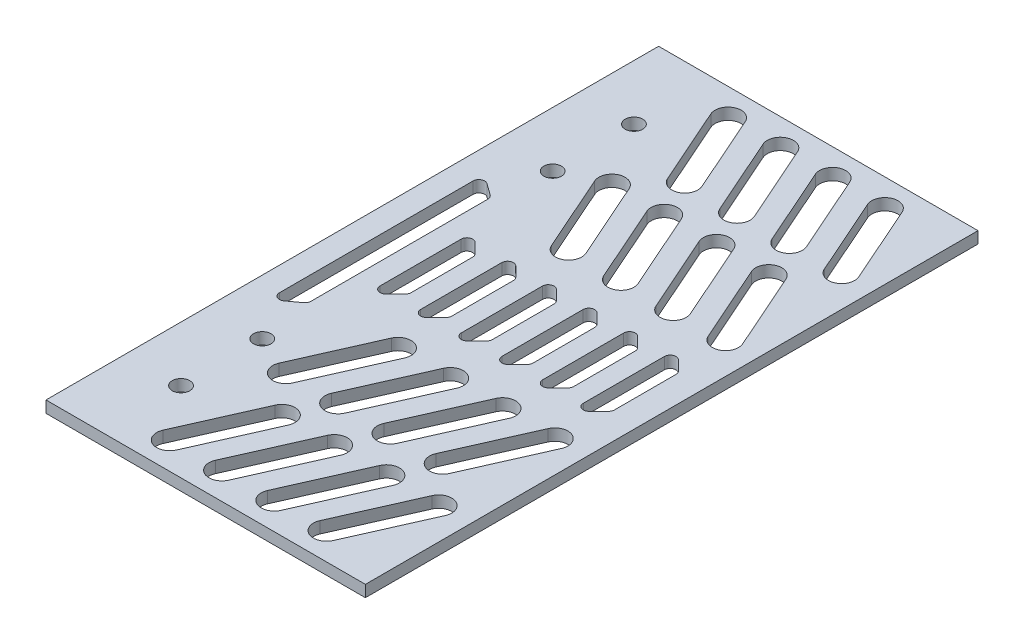
SolidWorks part; units mm, degrees
material "Thornel Mat VMA"
ref_plane "前视基准面" through (0, 0, 0) normal (0, 0, 1) x (1, 0, 0)
ref_plane "上视基准面" through (0, 0, 0) normal (0, 1, 0) x (1, 0, 0)
ref_plane "右视基准面" through (0, 0, 0) normal (1, 0, 0) x (0, 0, -1)
sketch "草图1" plane through (0, 0, 0) normal (0, 0, 1) x (1, 0, 0)
  line L2 (0, 30) -> (-55, 30)
  line L3 (0, 28) -> (-55, 28)
  line L4 (-55, 28) -> (-55, 30)
  line L5 (0, 0) -> (0, 30) construction
  line L6 (0, 30) -> (0, 28)
  dimension "D1" = 55
  dimension "D2" = 2
extrude "凸台-拉伸1" add sketch "草图1" along normal blind 105.5
sketch "草图2" plane through (0, 30, 0) normal (0, 1, 0) x (1, 0, 0)
  line L0 (-55, -105.5) -> (-55, 0) construction
  line L1 (0, -105.5) -> (-55, -105.5) construction
  line L2 (0, 0) -> (-55, 0) construction
  line L3 (-115.243, -52.75) -> (60.545, -52.75) construction
  line L4 (0, -105.5) -> (-55, -105.5) construction
  line L5 (-11.361, -4.6755) -> (-5.4387, -18.0556) construction
  line L6 (-9.3031, -3.7646) -> (-3.3807, -17.1447)
  line L7 (-13.419, -5.5864) -> (-7.4967, -18.9665)
  line L8 (-20.361, -4.6755) -> (-14.4387, -18.0556) construction
  line L9 (-18.3031, -3.7646) -> (-12.3807, -17.1447)
  line L10 (-22.419, -5.5864) -> (-16.4967, -18.9665)
  line L11 (-29.361, -4.6755) -> (-23.4387, -18.0556) construction
  line L12 (-27.3031, -3.7646) -> (-21.3807, -17.1447)
  line L13 (-31.419, -5.5864) -> (-25.4967, -18.9665)
  line L14 (-38.361, -4.6755) -> (-32.4387, -18.0556) construction
  line L15 (-36.3031, -3.7646) -> (-30.3807, -17.1447)
  line L16 (-40.419, -5.5864) -> (-34.4967, -18.9665)
  line L17 (-11.361, -24.6755) -> (-5.4387, -38.0556) construction
  line L18 (-9.3031, -23.7646) -> (-3.3807, -37.1447)
  line L19 (-13.419, -25.5864) -> (-7.4967, -38.9665)
  line L20 (-20.361, -24.6755) -> (-14.4387, -38.0556) construction
  line L21 (-18.3031, -23.7646) -> (-12.3807, -37.1447)
  line L22 (-22.419, -25.5864) -> (-16.4967, -38.9665)
  line L23 (-29.361, -24.6755) -> (-23.4387, -38.0556) construction
  line L24 (-27.3031, -23.7646) -> (-21.3807, -37.1447)
  line L25 (-31.419, -25.5864) -> (-25.4967, -38.9665)
  line L26 (-38.361, -24.6755) -> (-32.4387, -38.0556) construction
  line L27 (-36.3031, -23.7646) -> (-30.3807, -37.1447)
  line L28 (-40.419, -25.5864) -> (-34.4967, -38.9665)
  line L29 (-11.361, -80.8245) -> (-5.4387, -67.4444) construction
  line L30 (-9.3031, -81.7354) -> (-3.3807, -68.3553)
  line L31 (-13.419, -79.9136) -> (-7.4967, -66.5335)
  line L32 (-20.361, -80.8245) -> (-14.4387, -67.4444) construction
  line L33 (-18.3031, -81.7354) -> (-12.3807, -68.3553)
  line L34 (-22.419, -79.9136) -> (-16.4967, -66.5335)
  line L35 (-29.361, -80.8245) -> (-23.4387, -67.4444) construction
  line L36 (-27.3031, -81.7354) -> (-21.3807, -68.3553)
  line L37 (-31.419, -79.9136) -> (-25.4967, -66.5335)
  line L38 (-38.361, -80.8245) -> (-32.4387, -67.4444) construction
  line L39 (-36.3031, -81.7354) -> (-30.3807, -68.3553)
  line L40 (-40.419, -79.9136) -> (-34.4967, -66.5335)
  line L41 (-38.361, -100.8245) -> (-32.4387, -87.4444) construction
  line L42 (-36.3031, -101.7354) -> (-30.3807, -88.3553)
  line L43 (-40.419, -99.9136) -> (-34.4967, -86.5335)
  line L44 (-29.361, -100.8245) -> (-23.4387, -87.4444) construction
  line L45 (-27.3031, -101.7354) -> (-21.3807, -88.3553)
  line L46 (-31.419, -99.9136) -> (-25.4967, -86.5335)
  line L47 (-20.361, -100.8245) -> (-14.4387, -87.4444) construction
  line L48 (-18.3031, -101.7354) -> (-12.3807, -88.3553)
  line L49 (-22.419, -99.9136) -> (-16.4967, -86.5335)
  line L50 (-11.361, -100.8245) -> (-5.4387, -87.4444) construction
  line L51 (-9.3031, -101.7354) -> (-3.3807, -88.3553)
  line L52 (-13.419, -99.9136) -> (-7.4967, -86.5335)
  line L53 (-50.8884, -69.4318) -> (-50.8884, -36.0682)
  line L54 (-49.3025, -35.2578) -> (-47.3142, -36.6955)
  line L55 (-46.9001, -37.5059) -> (-46.9001, -67.9941)
  line L56 (-43.2424, -59.7286) -> (-43.2424, -45.7714)
  line L57 (-41.5353, -45.0643) -> (-39.857, -46.7426)
  line L58 (-39.5641, -47.4497) -> (-39.5641, -58.0503)
  line L59 (-41.5353, -60.4357) -> (-39.857, -58.7574)
  line L60 (-49.3025, -70.2422) -> (-47.3142, -68.8045)
  line L61 (-34.5353, -60.4357) -> (-32.857, -58.7574)
  line L62 (-36.2424, -59.7286) -> (-36.2424, -45.7714)
  line L63 (-34.5353, -45.0643) -> (-32.857, -46.7426)
  line L64 (-32.5641, -47.4497) -> (-32.5641, -58.0503)
  line L65 (-27.5353, -60.4357) -> (-25.857, -58.7574)
  line L66 (-29.2424, -59.7286) -> (-29.2424, -45.7714)
  line L67 (-27.5353, -45.0643) -> (-25.857, -46.7426)
  line L68 (-25.5641, -47.4497) -> (-25.5641, -58.0503)
  line L69 (-20.5353, -60.4357) -> (-18.857, -58.7574)
  line L70 (-22.2424, -59.7286) -> (-22.2424, -45.7714)
  line L71 (-20.5353, -45.0643) -> (-18.857, -46.7426)
  line L72 (-18.5641, -47.4497) -> (-18.5641, -58.0503)
  line L73 (-13.5353, -60.4357) -> (-11.857, -58.7574)
  line L74 (-15.2424, -59.7286) -> (-15.2424, -45.7714)
  line L75 (-13.5353, -45.0643) -> (-11.857, -46.7426)
  line L76 (-11.5641, -47.4497) -> (-11.5641, -58.0503)
  line L77 (-6.5353, -60.4357) -> (-4.857, -58.7574)
  line L78 (-8.2424, -59.7286) -> (-8.2424, -45.7714)
  line L79 (-6.5353, -45.0643) -> (-4.857, -46.7426)
  line L80 (-4.5641, -47.4497) -> (-4.5641, -58.0503)
  circle A0 centre (-45.5, -13.75) radius 1.51
  circle A1 centre (-45.5, -27.75) radius 1.51
  circle A2 centre (-45.5, -77.75) radius 1.51
  circle A3 centre (-45.5, -91.75) radius 1.51
  arc A4 (-9.3031, -3.7646) -> (-13.419, -5.5864) centre (-11.361, -4.6755) ccw
  arc A5 (-7.4967, -18.9665) -> (-3.3807, -17.1447) centre (-5.4387, -18.0556) ccw
  arc A6 (-18.3031, -3.7646) -> (-22.419, -5.5864) centre (-20.361, -4.6755) ccw
  arc A7 (-16.4967, -18.9665) -> (-12.3807, -17.1447) centre (-14.4387, -18.0556) ccw
  arc A8 (-27.3031, -3.7646) -> (-31.419, -5.5864) centre (-29.361, -4.6755) ccw
  arc A9 (-25.4967, -18.9665) -> (-21.3807, -17.1447) centre (-23.4387, -18.0556) ccw
  arc A10 (-36.3031, -3.7646) -> (-40.419, -5.5864) centre (-38.361, -4.6755) ccw
  arc A11 (-34.4967, -18.9665) -> (-30.3807, -17.1447) centre (-32.4387, -18.0556) ccw
  arc A12 (-9.3031, -23.7646) -> (-13.419, -25.5864) centre (-11.361, -24.6755) ccw
  arc A13 (-7.4967, -38.9665) -> (-3.3807, -37.1447) centre (-5.4387, -38.0556) ccw
  arc A14 (-18.3031, -23.7646) -> (-22.419, -25.5864) centre (-20.361, -24.6755) ccw
  arc A15 (-16.4967, -38.9665) -> (-12.3807, -37.1447) centre (-14.4387, -38.0556) ccw
  arc A16 (-27.3031, -23.7646) -> (-31.419, -25.5864) centre (-29.361, -24.6755) ccw
  arc A17 (-25.4967, -38.9665) -> (-21.3807, -37.1447) centre (-23.4387, -38.0556) ccw
  arc A18 (-36.3031, -23.7646) -> (-40.419, -25.5864) centre (-38.361, -24.6755) ccw
  arc A19 (-34.4967, -38.9665) -> (-30.3807, -37.1447) centre (-32.4387, -38.0556) ccw
  arc A20 (-9.3031, -81.7354) -> (-13.419, -79.9136) centre (-11.361, -80.8245) cw
  arc A21 (-7.4967, -66.5335) -> (-3.3807, -68.3553) centre (-5.4387, -67.4444) cw
  arc A22 (-18.3031, -81.7354) -> (-22.419, -79.9136) centre (-20.361, -80.8245) cw
  arc A23 (-16.4967, -66.5335) -> (-12.3807, -68.3553) centre (-14.4387, -67.4444) cw
  arc A24 (-27.3031, -81.7354) -> (-31.419, -79.9136) centre (-29.361, -80.8245) cw
  arc A25 (-25.4967, -66.5335) -> (-21.3807, -68.3553) centre (-23.4387, -67.4444) cw
  arc A26 (-36.3031, -81.7354) -> (-40.419, -79.9136) centre (-38.361, -80.8245) cw
  arc A27 (-34.4967, -66.5335) -> (-30.3807, -68.3553) centre (-32.4387, -67.4444) cw
  arc A28 (-36.3031, -101.7354) -> (-40.419, -99.9136) centre (-38.361, -100.8245) cw
  arc A29 (-34.4967, -86.5335) -> (-30.3807, -88.3553) centre (-32.4387, -87.4444) cw
  arc A30 (-27.3031, -101.7354) -> (-31.419, -99.9136) centre (-29.361, -100.8245) cw
  arc A31 (-25.4967, -86.5335) -> (-21.3807, -88.3553) centre (-23.4387, -87.4444) cw
  arc A32 (-18.3031, -101.7354) -> (-22.419, -99.9136) centre (-20.361, -100.8245) cw
  arc A33 (-16.4967, -86.5335) -> (-12.3807, -88.3553) centre (-14.4387, -87.4444) cw
  arc A34 (-9.3031, -101.7354) -> (-13.419, -99.9136) centre (-11.361, -100.8245) cw
  arc A35 (-7.4967, -86.5335) -> (-3.3807, -88.3553) centre (-5.4387, -87.4444) cw
  arc A36 (-47.3142, -36.6955) -> (-46.9001, -37.5059) centre (-47.9001, -37.5059) cw
  arc A37 (-50.8884, -36.0682) -> (-49.3025, -35.2578) centre (-49.8884, -36.0682) cw
  arc A38 (-39.5641, -47.4497) -> (-39.857, -46.7426) centre (-40.5641, -47.4497) ccw
  arc A39 (-41.5353, -45.0643) -> (-43.2424, -45.7714) centre (-42.2424, -45.7714) ccw
  arc A40 (-39.5641, -58.0503) -> (-39.857, -58.7574) centre (-40.5641, -58.0503) cw
  arc A41 (-41.5353, -60.4357) -> (-43.2424, -59.7286) centre (-42.2424, -59.7286) cw
  arc A42 (-47.3142, -68.8045) -> (-46.9001, -67.9941) centre (-47.9001, -67.9941) ccw
  arc A43 (-50.8884, -69.4318) -> (-49.3025, -70.2422) centre (-49.8884, -69.4318) ccw
  arc A44 (-32.5641, -58.0503) -> (-32.857, -58.7574) centre (-33.5641, -58.0503) cw
  arc A45 (-34.5353, -60.4357) -> (-36.2424, -59.7286) centre (-35.2424, -59.7286) cw
  arc A46 (-34.5353, -45.0643) -> (-36.2424, -45.7714) centre (-35.2424, -45.7714) ccw
  arc A47 (-32.5641, -47.4497) -> (-32.857, -46.7426) centre (-33.5641, -47.4497) ccw
  arc A48 (-25.5641, -58.0503) -> (-25.857, -58.7574) centre (-26.5641, -58.0503) cw
  arc A49 (-27.5353, -60.4357) -> (-29.2424, -59.7286) centre (-28.2424, -59.7286) cw
  arc A50 (-27.5353, -45.0643) -> (-29.2424, -45.7714) centre (-28.2424, -45.7714) ccw
  arc A51 (-25.5641, -47.4497) -> (-25.857, -46.7426) centre (-26.5641, -47.4497) ccw
  arc A52 (-18.5641, -58.0503) -> (-18.857, -58.7574) centre (-19.5641, -58.0503) cw
  arc A53 (-20.5353, -60.4357) -> (-22.2424, -59.7286) centre (-21.2424, -59.7286) cw
  arc A54 (-20.5353, -45.0643) -> (-22.2424, -45.7714) centre (-21.2424, -45.7714) ccw
  arc A55 (-18.5641, -47.4497) -> (-18.857, -46.7426) centre (-19.5641, -47.4497) ccw
  arc A56 (-11.5641, -58.0503) -> (-11.857, -58.7574) centre (-12.5641, -58.0503) cw
  arc A57 (-13.5353, -60.4357) -> (-15.2424, -59.7286) centre (-14.2424, -59.7286) cw
  arc A58 (-13.5353, -45.0643) -> (-15.2424, -45.7714) centre (-14.2424, -45.7714) ccw
  arc A59 (-11.5641, -47.4497) -> (-11.857, -46.7426) centre (-12.5641, -47.4497) ccw
  arc A60 (-4.5641, -58.0503) -> (-4.857, -58.7574) centre (-5.5641, -58.0503) cw
  arc A61 (-6.5353, -60.4357) -> (-8.2424, -59.7286) centre (-7.2424, -59.7286) cw
  arc A62 (-6.5353, -45.0643) -> (-8.2424, -45.7714) centre (-7.2424, -45.7714) ccw
  arc A63 (-4.5641, -47.4497) -> (-4.857, -46.7426) centre (-5.5641, -47.4497) ccw
  point P20 (-8.3999, -11.3655)
  point P28 (-17.3999, -11.3655)
  point P35 (-26.3999, -11.3655)
  point P42 (-35.3999, -11.3655)
  point P49 (-8.3999, -31.3655)
  point P56 (-17.3999, -31.3655)
  point P63 (-26.3999, -31.3655)
  point P70 (-35.3999, -31.3655)
  point P76 (-8.3999, -74.1345)
  point P83 (-17.3999, -74.1345)
  point P90 (-26.3999, -74.1345)
  point P97 (-35.3999, -74.1345)
  point P104 (-35.3999, -94.1345)
  point P111 (-26.3999, -94.1345)
  point P118 (-17.3999, -94.1345)
  point P125 (-8.3999, -94.1345)
  point P147 (-39.5641, -52.75)
  point P152 (-43.2424, -52.75)
  point P153 (-50.8884, -52.75)
  point P154 (-46.9001, -52.75)
  dimension "D1" = 9.5
  dimension "D12" = 1
  dimension "D13" = 1
  dimension "D2" = 9.5
  dimension "D3" = 9.5
  dimension "D4" = 9.5
  dimension "D5" = 14
  dimension "D6" = 14
  dimension "D7" = 13.75
  dimension "D8" = 13.75
  dimension "D9" = 52.75
  dimension "D10" = 4
  dimension "D11" = 2
  dimension "D14" = 6
extrude "切除-拉伸1" cut sketch "草图2" against normal through all
